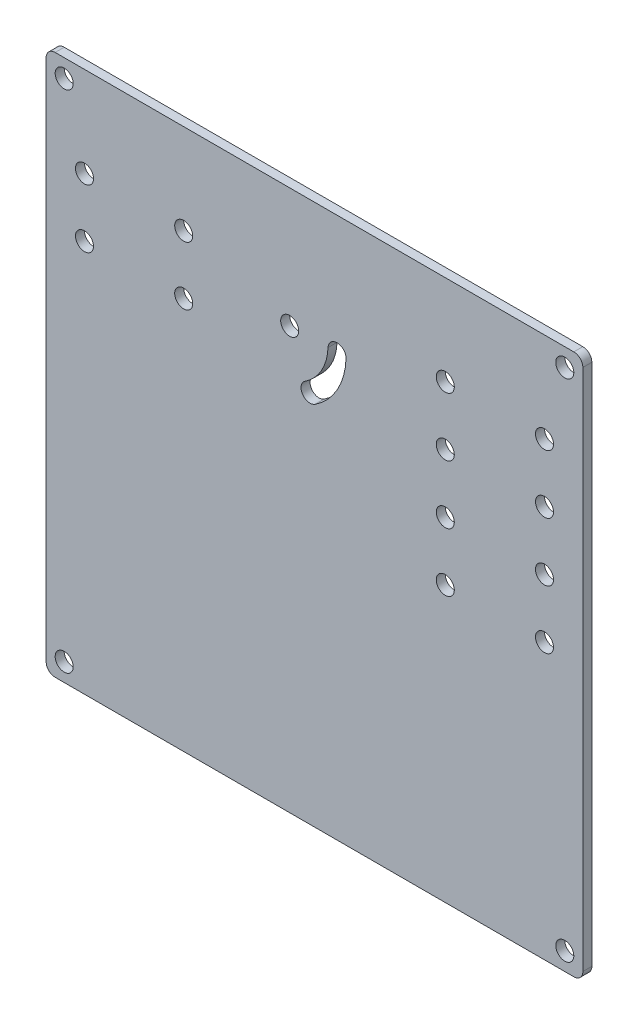
SolidWorks part; units mm, degrees
ref_plane "前视基准面" through (0, 0, 0) normal (0, 0, 1) x (1, 0, 0)
ref_plane "上视基准面" through (0, 0, 0) normal (0, 1, 0) x (1, 0, 0)
ref_plane "右视基准面" through (0, 0, 0) normal (1, 0, 0) x (0, 0, -1)
other "Configuration Table"
sketch "草图2" plane through (0, 0, 0) normal (0, 0, 1) x (1, 0, 0)
  line L1 (0, 0) -> (119, 0)
  line L2 (0, 0) -> (0, 120)
  line L3 (0, 120) -> (119, 120)
  line L4 (119, 0) -> (119, 120)
  dimension "D1" = 119
  dimension "D2" = 120
extrude "凸台-拉伸1" add sketch "草图2" along normal blind 2 contours L3 L4 L1 L2
sketch "草图4" plane through (0, 0, 2) normal (0, 0, 1) x (1, 0, 0)
  line L0 (0, 0) -> (0, 120) construction
  line L1 (8.5, 100) -> (30.5, 100) construction
  line L2 (8.5, 100) -> (8.5, 87) construction
  line L3 (8.5, 87) -> (30.5, 87) construction
  line L4 (30.5, 100) -> (30.5, 87) construction
  line L5 (119, 0) -> (119, 120) construction
  line L6 (54, 76.8623) -> (64.5, 76.8623) construction
  line L7 (54, 76.8623) -> (54, 93.5) construction
  line L8 (54, 93.5) -> (64.5, 93.5) construction
  line L9 (64.5, 76.8623) -> (64.5, 93.5) construction
  line L10 (88.5, 100) -> (110.5, 100) construction
  line L11 (88.5, 100) -> (88.5, 87) construction
  line L12 (88.5, 87) -> (110.5, 87) construction
  line L13 (110.5, 100) -> (110.5, 87) construction
  line L14 (88.5, 74) -> (110.5, 74) construction
  line L15 (88.5, 74) -> (88.5, 61) construction
  line L16 (88.5, 61) -> (110.5, 61) construction
  line L17 (110.5, 74) -> (110.5, 61) construction
  line L18 (0, 120) -> (119, 120) construction
  dimension "D1" = 8.5
  dimension "D2" = 22
  dimension "D3" = 13
  dimension "D4" = 23.5
  dimension "D5" = 10.5
  dimension "D6" = 8.5
  dimension "D7" = 22
  dimension "D8" = 13
  dimension "D9" = 22
  dimension "D10" = 13
  dimension "D11" = 8.5
  dimension "D12" = 6.5
  dimension "D13" = 20
  dimension "D14" = 0
  dimension "D15" = 13
sketch "草图6" plane through (0, 0, 0) normal (0, 0, 1) x (1, 0, 0)
  circle A0 centre (8.5, 100) radius 2
  circle A1 centre (30.5, 100) radius 2
  circle A2 centre (8.5, 87) radius 2
  circle A3 centre (30.5, 87) radius 2
  circle A4 centre (54, 93.5) radius 2
  circle A5 centre (88.5, 100) radius 2
  circle A6 centre (88.5, 87) radius 2
  circle A7 centre (110.5, 100) radius 2
  circle A8 centre (110.5, 87) radius 2
  circle A9 centre (88.5, 74) radius 2
  circle A10 centre (88.5, 61) radius 2
  circle A11 centre (110.5, 74) radius 2
  circle A12 centre (110.5, 61) radius 2
  dimension "D1" = 4
extrude "切除-拉伸3" cut sketch "草图6" along normal blind 2
sketch "草图7" plane through (0, 0, 0) normal (0, 0, 1) x (1, 0, 0)
  arc A1 (64.5, 93.5) -> (58.5211, 82.9054) centre (51.2464, 93.9951) cw construction
  arc A2 (59.6181, 81.2331) -> (66.4986, 93.4253) centre (51.2464, 93.9951) ccw
  arc A3 (57.4241, 84.5777) -> (62.5014, 93.5747) centre (51.2464, 93.9951) ccw
  arc A4 (57.4241, 84.5777) -> (59.6181, 81.2331) centre (58.5211, 82.9054) ccw
  arc A6 (62.5014, 93.5747) -> (66.4986, 93.4253) centre (64.5, 93.5) cw
  point P5 (62.7969, 87.4768)
  dimension "D2" = 15.2628
extrude "切除-拉伸5" cut sketch "草图7" along normal blind 2
fillet "圆角1" radius 2 4 edges at (119, 120, 1) (119, 0, 1) (0, 0, 1) (0, 120, 1)
sketch "草图9" plane through (0, 0, 2) normal (0, 0, 1) x (1, 0, 0)
  line L0 (2, 120) -> (117, 120) construction
  line L1 (4, 116) -> (115, 116) construction
  line L2 (4, 116) -> (4, 4) construction
  line L3 (4, 4) -> (115, 4) construction
  line L4 (115, 116) -> (115, 4) construction
  line L5 (0, 2) -> (0, 118) construction
  line L7 (119, 2) -> (119, 118) construction
  line L8 (2, 0) -> (117, 0) construction
  circle A0 centre (4, 116) radius 2
  circle A1 centre (115, 116) radius 2
  circle A2 centre (4, 4) radius 2
  circle A3 centre (115, 4) radius 2
  dimension "D5" = 4
  dimension "D6" = 4
  dimension "D7" = 4
  dimension "D8" = 4
  dimension "D1" = 4
  dimension "D2" = 4
  dimension "D3" = 4
  dimension "D4" = 4
extrude "切除-拉伸6" cut sketch "草图9" against normal blind 2
sketch "草图11" plane through (0, 0, 2) normal (0, 0, 1) x (1, 0, 0)
  circle A0 centre (110.5, 87) radius 2 construction
  circle A1 centre (110.5, 100) radius 2 construction
  circle A2 centre (88.5, 87) radius 2 construction
  circle A3 centre (88.5, 100) radius 2 construction
  arc A4 (57.4241, 84.5777) -> (59.6181, 81.2331) centre (58.5211, 82.9054) ccw construction
  arc A5 (59.6181, 81.2331) -> (66.4986, 93.4253) centre (51.2464, 93.9951) ccw construction
  arc A6 (66.4986, 93.4253) -> (62.5014, 93.5747) centre (64.5, 93.5) ccw construction
  arc A7 (57.4241, 84.5777) -> (62.5014, 93.5747) centre (51.2464, 93.9951) ccw construction
  circle A8 centre (54, 93.5) radius 2 construction
  circle A9 centre (30.5, 87) radius 2 construction
  circle A10 centre (30.5, 100) radius 2 construction
  circle A11 centre (8.5, 87) radius 2 construction
  circle A12 centre (8.5, 100) radius 2 construction
  circle A13 centre (110.5, 87) radius 2
  circle A14 centre (110.5, 100) radius 2
  circle A15 centre (88.5, 87) radius 2
  circle A16 centre (88.5, 100) radius 2
  arc A17 (57.4241, 84.5777) -> (59.6181, 81.2331) centre (58.5211, 82.9054) ccw
  arc A18 (59.6181, 81.2331) -> (66.4986, 93.4253) centre (51.2464, 93.9951) ccw
  arc A19 (66.4986, 93.4253) -> (62.5014, 93.5747) centre (64.5, 93.5) ccw
  arc A20 (57.4241, 84.5777) -> (62.5014, 93.5747) centre (51.2464, 93.9951) ccw
  circle A21 centre (54, 93.5) radius 2
  circle A22 centre (30.5, 87) radius 2
  circle A23 centre (30.5, 100) radius 2
  circle A24 centre (8.5, 87) radius 2
  circle A25 centre (8.5, 100) radius 2
